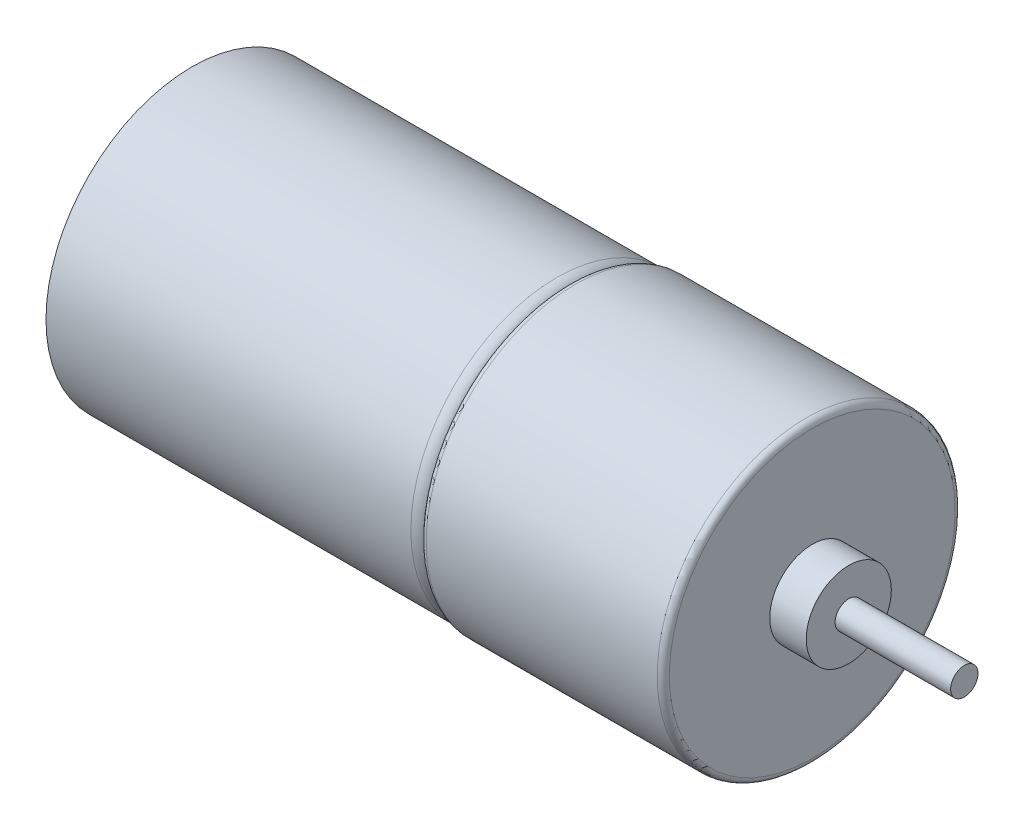
SolidWorks part; units mm, degrees
ref_plane "Front Plane" through (0, 0, 0) normal (0, 0, 1) x (1, 0, 0)
ref_plane "Top Plane" through (0, 0, 0) normal (0, 1, 0) x (1, 0, 0)
ref_plane "Right Plane" through (0, 0, 0) normal (1, 0, 0) x (0, 0, -1)
sketch "Sketch1" plane through (0, 0, 0) normal (1, 0, 0) x (0, 0, -1)
  circle A0 centre (0, 0) radius 12
  dimension "D1" = 24
extrude "Boss-Extrude1" add sketch "Sketch1" along normal blind 31
fillet "Fillet1" radius 1 1 edges at (31, 0, -12)
sketch "Sketch2" plane through (0, 0, 0) normal (-1, 0, 0) x (0, 0, 1)
  circle A2 centre (0, 0) radius 11.5
  circle A3 centre (0, 0) radius 11.5
  dimension "D1" = 0.5
extrude "Cut-Extrude1" cut sketch "Sketch2" against normal blind 1
sketch "Sketch3" plane through (31, 0, 0) normal (1, 0, 0) x (0, 0, -1)
  circle A0 centre (0, 0) radius 12.25
  dimension "D1" = 24.5
extrude "Boss-Extrude2" add sketch "Sketch3" along normal blind 20
fillet "Fillet2" radius 0.5 2 edges at (51, 0, -12.25) (31, 0, -12.25)
sketch "Sketch4" plane through (51, 0, 0) normal (1, 0, 0) x (0, 0, -1)
  circle A0 centre (0, 0) radius 3.5
  dimension "D1" = 7
extrude "Boss-Extrude3" add sketch "Sketch4" along normal blind 3
sketch "Sketch5" plane through (54, 0, 0) normal (1, 0, 0) x (0, 0, -1)
  circle A0 centre (0, 0) radius 1.1255
extrude "Boss-Extrude4" add sketch "Sketch5" along normal blind 9.5
sketch "Sketch6" plane through (1, 0, 0) normal (-1, 0, 0) x (0, 0, 1)
  point P0 (0, 0)
